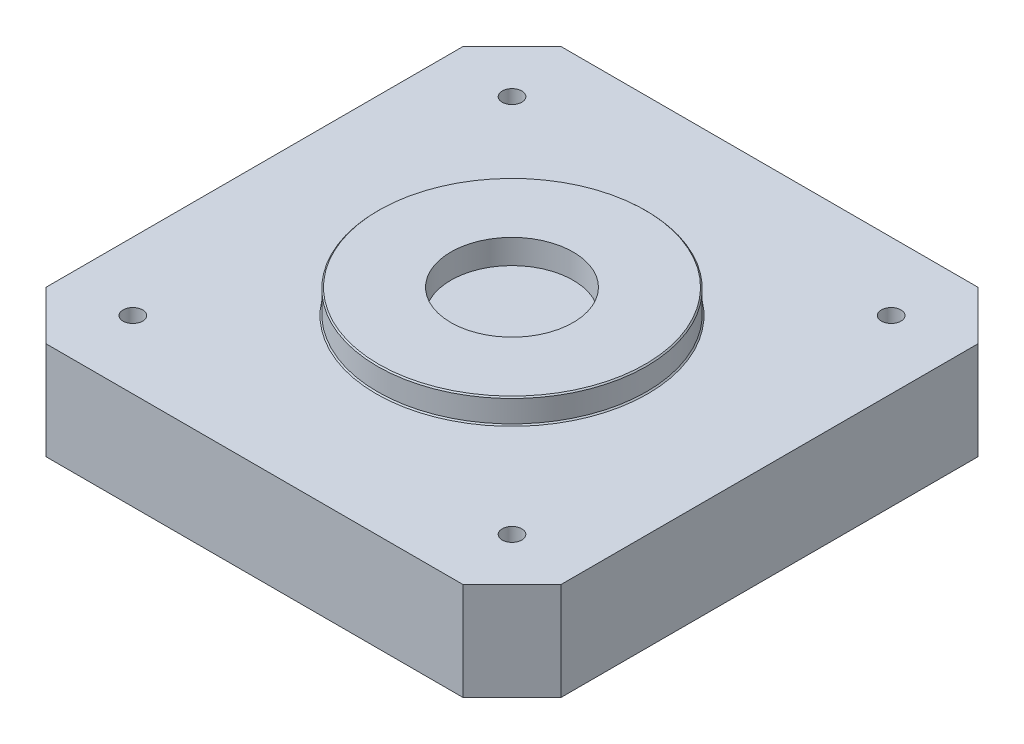
SolidWorks part; units mm, degrees
ref_plane "Front" through (0, 0, 0) normal (0, 0, 1) x (1, 0, 0)
ref_plane "Top" through (0, 0, 0) normal (0, 1, 0) x (1, 0, 0)
ref_plane "Right" through (0, 0, 0) normal (1, 0, 0) x (0, 0, -1)
sketch "Sketch1" plane through (0, 0, 0) normal (0, 1, 0) x (1, 0, 0)
  line L1 (-21.05, -21.05) -> (21.05, -21.05)
  line L2 (-21.05, -21.05) -> (-21.05, 21.05)
  line L3 (-21.05, 21.05) -> (21.05, 21.05)
  line L4 (21.05, -21.05) -> (21.05, 21.05)
  line L5 (-21.05, -21.05) -> (21.05, 21.05) construction
  line L6 (-21.05, 21.05) -> (21.05, -21.05) construction
  point P0 (0, 0)
  dimension "D1" = 42.1
extrude "Boss-Extrude1" add sketch "Sketch1" along normal blind 8
chamfer "Chamfer1" distance 4 angle 45 4 edges at (-21.05, 4, -21.05) (-21.05, 4, 21.05) (21.05, 4, -21.05) (21.05, 4, 21.05)
sketch "Sketch2" plane through (0, 8, 0) normal (0, 1, 0) x (1, 0, 0)
  circle A0 centre (0, 0) radius 11
  circle A1 centre (0, 0) radius 5
  dimension "D1" = 22
  dimension "D2" = 10
extrude "Boss-Extrude2" add sketch "Sketch2" along normal blind 2
chamfer "Chamfer2" distance 0.1 angle 45 2 edges at (0, 10, 11) (0, 8, -11)
sketch "Sketch3" plane through (0, 8, 0) normal (0, 1, 0) x (1, 0, 0)
  line L1 (-15.5, -15.5) -> (15.5, -15.5) construction
  line L2 (-15.5, -15.5) -> (-15.5, 15.5) construction
  line L3 (-15.5, 15.5) -> (15.5, 15.5) construction
  line L4 (15.5, -15.5) -> (15.5, 15.5) construction
  line L5 (-15.5, -15.5) -> (15.5, 15.5) construction
  line L6 (-15.5, 15.5) -> (15.5, -15.5) construction
  point P0 (0, 0)
  dimension "D1" = 31
hole_wizard "M2x0.4 Tapped Hole1" positions "3DSketch1" profile "Sketch4" tap size "M2x0.4" standard "ANSI Metric"
sketch3d "3DSketch1"
  point P0 (-15.5, 8, -15.5)
  point P3 (15.5, 8, -15.5)
  point P6 (15.5, 8, 15.5)
  point P9 (-15.5, 8, 15.5)
sketch "Sketch4" plane through (-15.5, 8, -15.5) normal (1, 0, 0) x (0, 0, 1)
  line L0 (0, 0) -> (0, 8.4807)
  line L1 (0, 8.4807) -> (0.8, 8)
  line L2 (0.8, 8) -> (0.8, 0)
  line L5 (0.8, 0) -> (0, 0)
  line L10 (0, 8.4807) -> (-0.8, 8) construction
  line L11 (0, -6.35) -> (0, 107.95) construction
  dimension "Tap Drill Dia." = 1.6
  dimension "Tap Drill Depth" = 8
  dimension "Drill Angle" = 118
cosmetic thread "Hole Thread1" parameters "D1"=5, "D2"=2
cosmetic thread "Hole Thread2" parameters "D1"=5, "D2"=2
cosmetic thread "Hole Thread3" parameters "D1"=5, "D2"=2
cosmetic thread "Hole Thread4" parameters "D1"=5, "D2"=2
